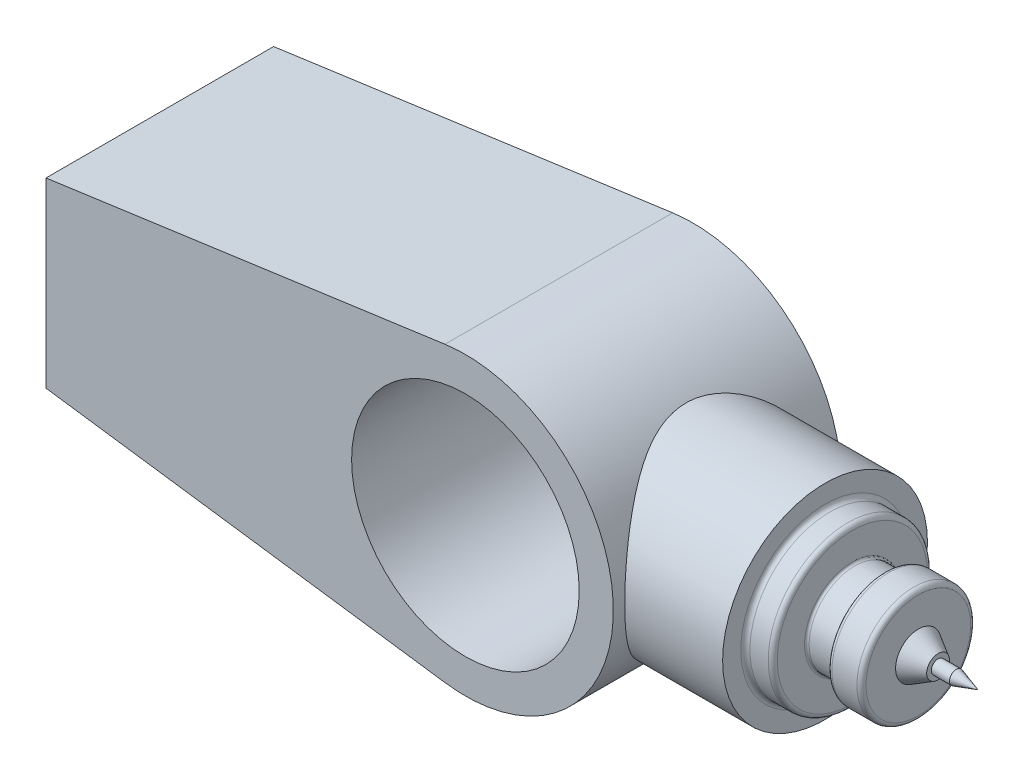
SolidWorks part; units mm, degrees
material "ABS"
ref_plane "Front Plane" through (0, 0, 0) normal (0, 0, 1) x (1, 0, 0)
ref_plane "Top Plane" through (0, 0, 0) normal (0, 1, 0) x (1, 0, 0)
ref_plane "Right Plane" through (0, 0, 0) normal (1, 0, 0) x (0, 0, -1)
sketch "Sketch1" plane through (0, 0, 0) normal (0, 0, 1) x (1, 0, 0)
  line L0 (-184.2564, 40) -> (-184.2564, -40)
  line L1 (-8.9537, 64.3804) -> (-184.2564, 40)
  line L2 (-184.2564, -40) -> (-8.9537, -64.3804)
  arc A0 (-8.9537, -64.3804) -> (-8.9537, 64.3804) centre (0, 0) ccw
  circle A1 centre (0, 0) radius 50
  point P5 (-184.2564, 0)
  dimension "D1" = 130
  dimension "D3" = 100
  dimension "D2" = 80
extrude "Boss-Extrude1" add sketch "Sketch1" along normal mid plane 100
ref_plane "Plane1" through (120, 0, 0) normal (1, 0, 0) x (0, 0, -1)
sketch "Sketch2" plane through (120, 0, 0) normal (1, 0, 0) x (0, 0, -1)
  circle A0 centre (0, 0) radius 45
  dimension "D1" = 90
extrude "Boss-Extrude2" add sketch "Sketch2" against normal up to next
sketch "Sketch3" plane through (0, 0, 0) normal (0, 0, 1) x (1, 0, 0)
  line L0 (0, 0) -> (175.1996, 0) construction
  line L1 (120, 0) -> (120, -20)
  line L2 (120, -45) -> (120, 45) construction
  line L3 (120, -20) -> (134, -20)
  line L4 (134, -20) -> (134, -25)
  line L5 (134, -25) -> (149, -25)
  line L6 (149, -25) -> (149, -10)
  line L7 (149, -10) -> (157.6603, -5)
  line L9 (157.6603, -5) -> (157.6603, -3)
  line L10 (157.6603, -3) -> (165.6603, -3)
  line L11 (120, 0) -> (175.1996, 0)
  line L12 (165.6603, -3) -> (175.1996, 0)
  line L13 (175.3427, 0) -> (298.6471, 0) construction
  dimension "D1" = 20
  dimension "D2" = 14
  dimension "D3" = 5
  dimension "D4" = 15
  dimension "D5" = 10
  dimension "D6" = 120
  dimension "D7" = 8
  dimension "D8" = 10
revolve "Revolve1" add sketch "Sketch3" angle 360 about L0
sketch "Sketch4" plane through (120, 0, 0) normal (1, 0, 0) x (0, 0, -1)
  circle A2 centre (0, 0) radius 45
  circle A3 centre (0, 0) radius 35
  dimension "D1" = 70
extrude "Cut-Extrude2" cut sketch "Sketch4" against normal blind 12
fillet "Fillet1" radius 2 4 edges at (120, 0, -35) (108, 0, -35) (149, 0, 25) (134, 0, 25)
fillet "Fillet2" radius 1 2 edges at (120, 0, 20) (134, 0, 20)
